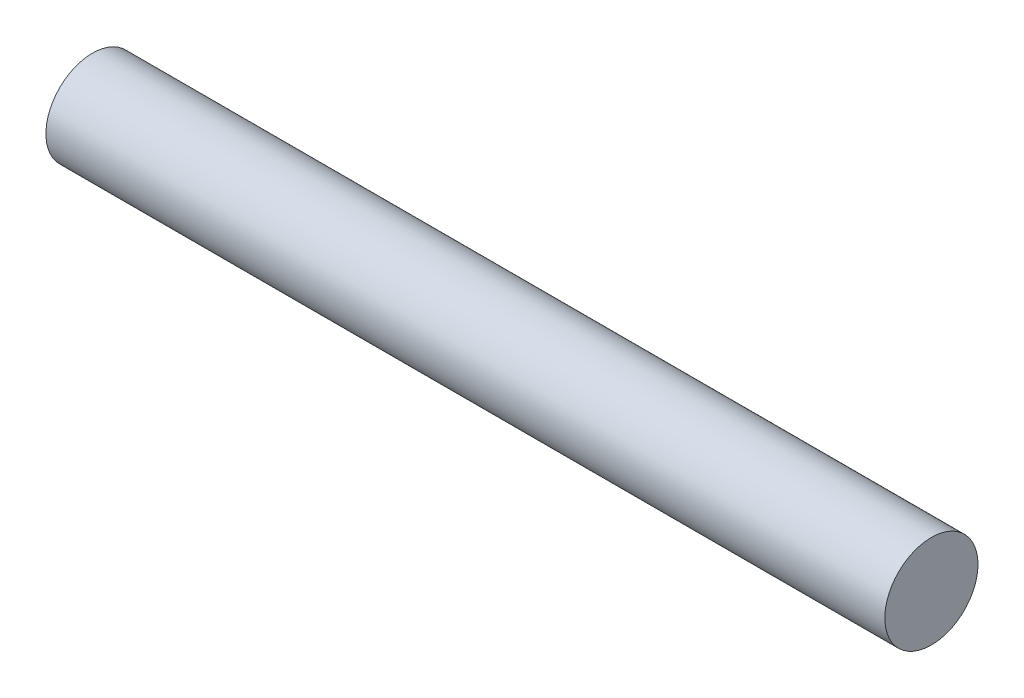
SolidWorks part; units mm, degrees
ref_plane "Front Plane" through (0, 0, 0) normal (0, 0, 1) x (1, 0, 0)
ref_plane "Top Plane" through (0, 0, 0) normal (0, 1, 0) x (1, 0, 0)
ref_plane "Right Plane" through (0, 0, 0) normal (1, 0, 0) x (0, 0, -1)
sketch "Sketch1" plane through (0, 0, 0) normal (1, 0, 0) x (0, 0, -1)
  circle A0 centre (0, 0) radius 1
  dimension "D1" = 2
extrude "Boss-Extrude1" add sketch "Sketch1" along normal mid plane 18
